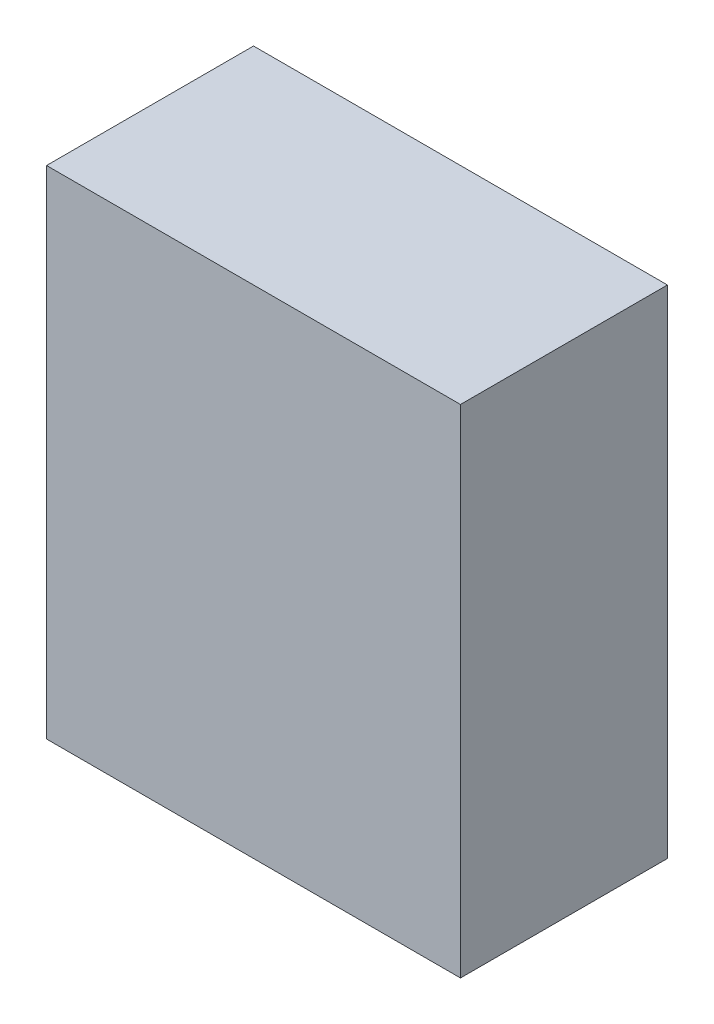
SolidWorks part; units mm, degrees
ref_plane "Front Plane" through (0, 0, 0) normal (0, 0, 1) x (1, 0, 0)
ref_plane "Top Plane" through (0, 0, 0) normal (0, 1, 0) x (1, 0, 0)
ref_plane "Right Plane" through (0, 0, 0) normal (1, 0, 0) x (0, 0, -1)
sketch "Sketch1" plane through (0, 0, 0) normal (0, 1, 0) x (1, 0, 0)
  line L1 (-25, -12.5) -> (25, -12.5)
  line L2 (-25, -12.5) -> (-25, 12.5)
  line L3 (-25, 12.5) -> (25, 12.5)
  line L4 (25, -12.5) -> (25, 12.5)
  line L5 (-25, -12.5) -> (25, 12.5) construction
  line L6 (-25, 12.5) -> (25, -12.5) construction
  point P0 (0, 0)
  dimension "D1" = 50
  dimension "D2" = 25
extrude "Boss-Extrude1" add sketch "Sketch1" along normal blind 60
ref_plane "Plane5" through (0, 0, 0) normal (-1, 0, 0) x (0, 0, 1)
sketch "Sketch7" plane through (0, 0, 0) normal (-1, 0, 0) x (0, 0, 1)
  line L0 (12.5, 60) -> (12.5, 0) construction
  line L1 (-12.5, 62.2743) -> (12.5, 62.2743)
  line L2 (-12.5, 62.2743) -> (-12.5, 54.0797)
  line L3 (-12.5, 54.0797) -> (12.5, 54.0797)
  line L4 (12.5, 62.2743) -> (12.5, 54.0797)
  dimension "D1" = 8.1946
  dimension "D2" = 2.2743
sketch "Sketch8" plane through (0, 0, 0) normal (-1, 0, 0) x (0, 0, 1)
  line L0 (-12.5, 60) -> (-12.5, 85.4)
  line L1 (-12.5, 85.4) -> (13.1735, 85.4)
  dimension "D1" = 25.4
